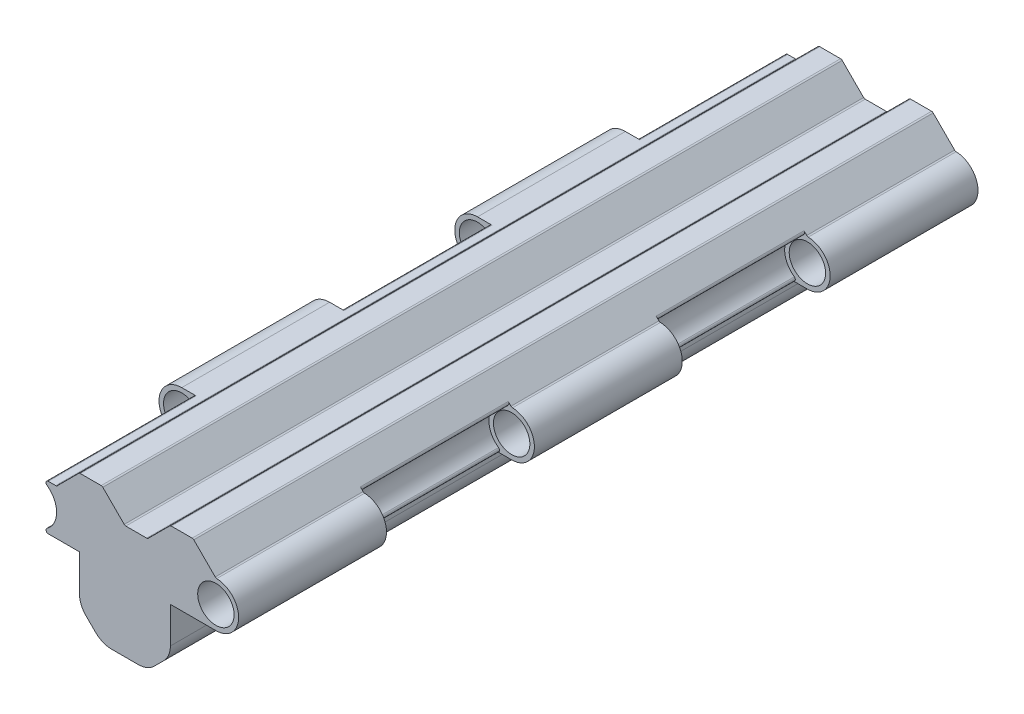
SolidWorks part; units mm, degrees
material "1023 Carbon Steel Sheet (SS)"
ref_plane "Front Plane" through (0, 0, 0) normal (0, 0, 1) x (1, 0, 0)
ref_plane "Top Plane" through (0, 0, 0) normal (0, 1, 0) x (1, 0, 0)
ref_plane "Right Plane" through (0, 0, 0) normal (1, 0, 0) x (0, 0, -1)
sketch "Sketch1" plane through (0, 0, 0) normal (0, 0, 1) x (1, 0, 0)
  line L1 (0, 0) -> (4, 0)
  line L2 (0, 0) -> (0, 4)
  line L3 (0, 4) -> (4, 4)
  line L4 (4, 0) -> (4, 4)
  dimension "D1" = 4
  dimension "D2" = 4
extrude "Boss-Extrude1" add sketch "Sketch1" along normal blind 32.5
chamfer "Chamfer1" distance 1 angle 45 2 edges at (0, 0, 16.25) (4, 0, 16.25)
fillet "Fillet1" radius 1 4 edges at (4, 1, 16.25) (0, 1, 16.25) (1, 0, 16.25) (3, 0, 16.25)
sketch "Sketch2" plane through (0, 0, 32.5) normal (0, 0, 1) x (1, 0, 0)
  line L2 (0, 4) -> (0, 3) construction
  line L3 (0, 4) -> (0, 1.4142) construction
  line L4 (0, 3) -> (-2, 3)
  line L7 (-2, 5) -> (-1, 5)
  line L8 (-1, 5) -> (0, 6)
  line L9 (0, 6) -> (1, 6)
  line L10 (1, 6) -> (2, 5)
  line L11 (2, 5) -> (3, 5)
  line L12 (3, 5) -> (4, 6)
  line L13 (4, 6) -> (5, 6)
  line L14 (5, 6) -> (6, 5)
  line L16 (6, 3) -> (0, 3)
  arc A0 (6, 5) -> (6, 3) centre (6, 4) ccw
  arc A1 (-2, 5) -> (-2, 3) centre (-2, 4) cw
extrude "Boss-Extrude7" add sketch "Sketch2" against normal blind 32.5 contours L16 L4 A1 L7 L8 L9 L10 L11 L12 L13 L14 A0
sketch "Sketch3" plane through (0, 0, 32.5) normal (0, 0, 1) x (1, 0, 0)
  line L3 (6, 5) -> (6, 3) construction
  circle A0 centre (6, 4) radius 1
extrude "Boss-Extrude9" add sketch "Sketch3" against normal blind 6.5
pattern_linear "LPattern2" count 3 spacing 13 along (0, 0, -1) of "Boss-Extrude9"
ref_plane "Plane1" through (0, 0, 26) normal (0, 0, 1) x (1, 0, 0)
sketch "Sketch5" plane through (0, 0, 26) normal (0, 0, 1) x (1, 0, 0)
  circle A0 centre (-2, 4) radius 1
extrude "Boss-Extrude10" add sketch "Sketch5" against normal blind 6.5
pattern_linear "LPattern3" count 2 spacing 13 along (0, 0, -1) of "Boss-Extrude10"
fillet "Fillet2" radius 0.1 10 edges at (-2, 3, 29.25) (-2, 3, 16.25) (-2, 5, 29.25) (-2, 5, 16.25) (-2, 3, 3.25) (-2, 5, 3.25) (6, 3, 9.75) (6, 5, 9.75) (6, 5, 22.75) (6, 3, 22.75)
hole_wizard "M2 Tapped Hole1" positions "Sketch6" profile "Sketch7" tap size "M2" standard "DIN" end condition through all
sketch "Sketch6" plane through (0, 0, 0) normal (0, 0, -1) x (-1, 0, 0)
  point P0 (-6, 4)
  point P3 (2, 4)
sketch "Sketch7" plane through (6, 4, 0) normal (1, 0, 0) x (0, 1, 0)
  line L0 (0, 0) -> (0, 32.5)
  line L1 (0, 32.5) -> (0.8, 32.5)
  line L2 (0.8, 32.5) -> (0.8, 0)
  line L5 (0.8, 0) -> (0, 0)
  line L11 (0, -6.35) -> (0, 107.95) construction
  dimension "Thread Major Dia." = 1.6
  dimension "Thru Tap Drill Depth" = 32.5
fillet "Fillet3" radius 0.1 10 edges at (6, 5, 3.25) (6, 5, 16.25) (6, 5, 29.25) (-1, 5, 16.25) (5, 6, 16.25) (4, 6, 16.25) (3, 5, 16.25) (2, 5, 16.25) (1, 6, 16.25) (0, 6, 16.25)
